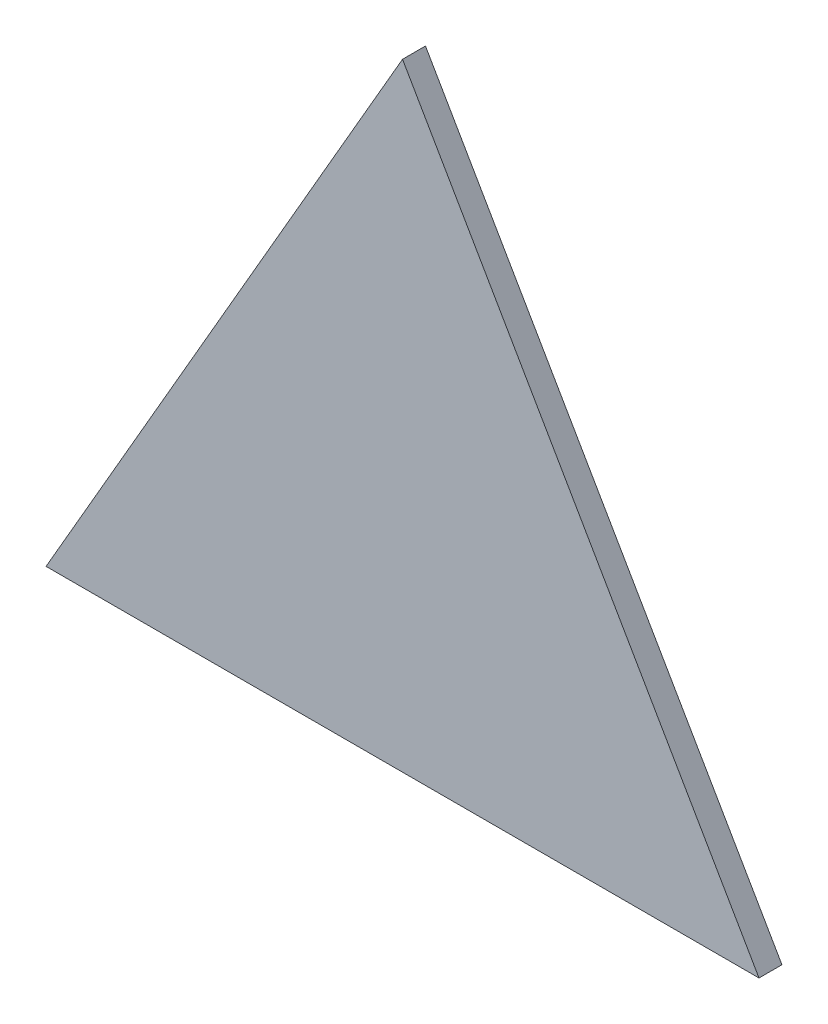
SolidWorks part; units mm, degrees
ref_plane "Front Plane" through (0, 0, 0) normal (0, 0, 1) x (1, 0, 0)
ref_plane "Top Plane" through (0, 0, 0) normal (0, 1, 0) x (1, 0, 0)
ref_plane "Right Plane" through (0, 0, 0) normal (1, 0, 0) x (0, 0, -1)
sketch "Sketch1" plane through (0, 0, 325.2315) normal (0, 0, -1) x (-1, 0, 0)
  line L0 (-279.7093, 340.3653) -> (-94.7086, 660.7959)
  line L1 (-94.7086, 660.7959) -> (90.2922, 340.3653)
  line L2 (90.2922, 340.3653) -> (-279.7093, 340.3653)
  arc A0 (-48.4584, 580.6883) -> (-140.9587, 580.6883) centre (-94.7086, 660.7959) cw construction
  arc A1 (-187.2089, 340.3653) -> (-233.4591, 420.4729) centre (-279.7093, 340.3653) ccw construction
  arc A2 (44.042, 420.4729) -> (-2.2082, 340.3653) centre (90.2922, 340.3653) ccw construction
extrude "Boss-Extrude1" add sketch "Sketch1" against normal blind 11.9062
